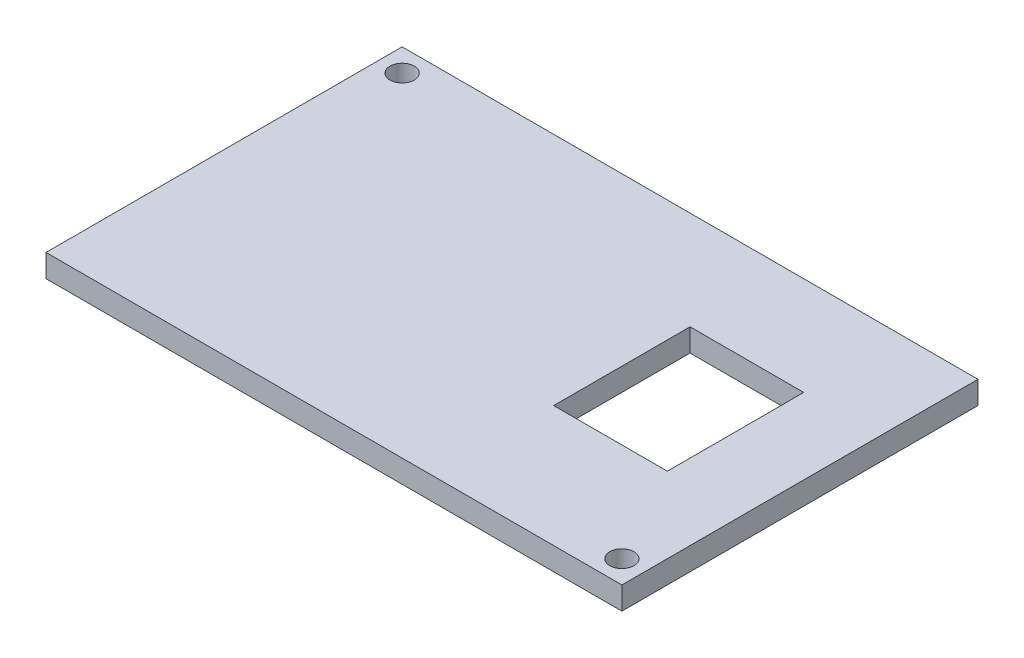
SolidWorks part; units mm, degrees
ref_plane "Front Plane" through (0, 0, 0) normal (0, 0, 1) x (1, 0, 0)
ref_plane "Top Plane" through (0, 0, 0) normal (0, 1, 0) x (1, 0, 0)
ref_plane "Right Plane" through (0, 0, 0) normal (1, 0, 0) x (0, 0, -1)
sketch "Sketch1" plane through (0, 0, 0) normal (0, 1, 0) x (1, 0, 0)
  line L1 (-546.907, 260.8809) -> (-622.907, 260.8809)
  line L2 (-546.907, 260.8809) -> (-546.907, 213.8809)
  line L3 (-546.907, 213.8809) -> (-622.907, 213.8809)
  line L4 (-622.907, 260.8809) -> (-622.907, 213.8809)
  dimension "D1" = 76
  dimension "D2" = 47
extrude "Boss-Extrude2" add sketch "Sketch1" along normal blind 3
sketch "Sketch2" plane through (0, 3, 0) normal (0, 1, 0) x (1, 0, 0)
  line L0 (-546.907, 260.8809) -> (-622.907, 260.8809) construction
  line L1 (-622.907, 260.8809) -> (-622.907, 213.8809) construction
  line L2 (-546.907, 213.8809) -> (-546.907, 260.8809) construction
  line L3 (-622.907, 213.8809) -> (-546.907, 213.8809) construction
  circle A0 centre (-619.907, 257.8809) radius 1.6
  circle A1 centre (-549.907, 216.8809) radius 1.6
  dimension "D1" = 3
  dimension "D3" = 3
  dimension "D2" = 3
  dimension "D4" = 3
extrude "Cut-Extrude1" cut sketch "Sketch2" against normal blind 3
sketch "Sketch3" plane through (0, 3, 0) normal (0, 1, 0) x (1, 0, 0)
  line L0 (-546.907, 213.8809) -> (-546.907, 260.8809) construction
  line L1 (-571.907, 247.8809) -> (-556.907, 247.8809)
  line L2 (-571.907, 247.8809) -> (-571.907, 229.8809)
  line L3 (-571.907, 229.8809) -> (-556.907, 229.8809)
  line L4 (-556.907, 247.8809) -> (-556.907, 229.8809)
  line L5 (-622.907, 213.8809) -> (-546.907, 213.8809) construction
  point P4 (-571.907, 238.8809)
  dimension "D1" = 15
  dimension "D2" = 15
  dimension "D3" = 18
  dimension "D4" = 10
  dimension "D5" = 16
extrude "Cut-Extrude3" cut sketch "Sketch3" against normal blind 3
